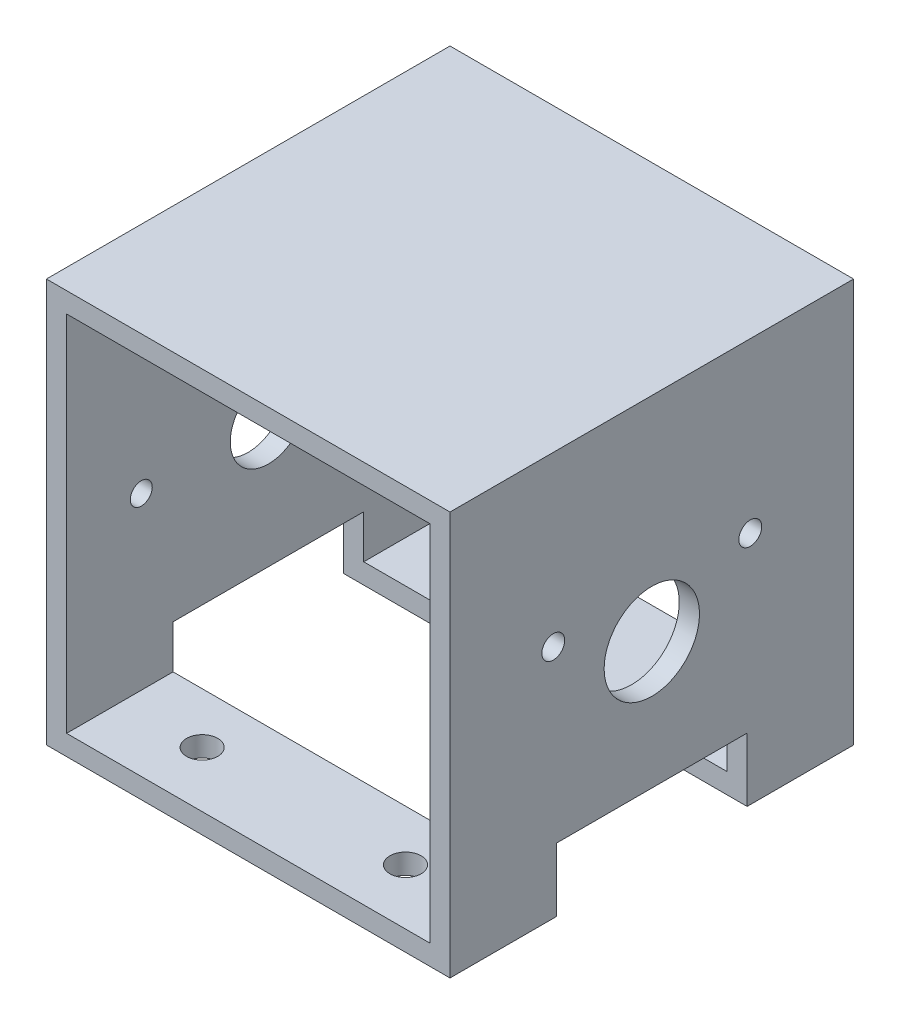
SolidWorks part; units mm, degrees
ref_plane "Front Plane" through (0, 0, 0) normal (0, 0, 1) x (1, 0, 0)
ref_plane "Top Plane" through (0, 0, 0) normal (0, 1, 0) x (1, 0, 0)
ref_plane "Right Plane" through (0, 0, 0) normal (1, 0, 0) x (0, 0, -1)
sketch "Sketch1" plane through (0, 0, 0) normal (0, 0, 1) x (1, 0, 0)
  line L1 (-31.75, -31.75) -> (31.75, -31.75)
  line L2 (-31.75, -31.75) -> (-31.75, 31.75)
  line L3 (-31.75, 31.75) -> (31.75, 31.75)
  line L4 (31.75, -31.75) -> (31.75, 31.75)
  line L5 (-31.75, -31.75) -> (31.75, 31.75) construction
  line L6 (-31.75, 31.75) -> (31.75, -31.75) construction
  point P0 (0, 0)
  dimension "D1" = 63.5
extrude "Extrude-Thin1" add sketch "Sketch1" along normal blind 63.5 thin thin type one direction reverse wall 3.175
sketch "Sketch2" plane through (31.75, 0, 0) normal (1, 0, 0) x (0, 0, -1)
  line L0 (-63.5, -31.75) -> (0, -31.75) construction
  line L1 (-16.75, -41.75) -> (-46.75, -41.75)
  line L2 (-16.75, -41.75) -> (-16.75, -21.75)
  line L3 (-16.75, -21.75) -> (-46.75, -21.75)
  line L4 (-46.75, -41.75) -> (-46.75, -21.75)
  line L5 (-16.75, -41.75) -> (-46.75, -21.75) construction
  line L6 (-16.75, -21.75) -> (-46.75, -41.75) construction
  point P0 (-31.75, -31.75)
  dimension "D1" = 30
  dimension "D2" = 10
extrude "Cut-Extrude1" cut sketch "Sketch2" against normal through all contours L1 L4 L3 L2
sketch "Sketch5" plane through (28.575, 11.8301, 29.9884) normal (-1, 0, 0) x (0, 0, 1)
  line L0 (1.7616, -13.5801) -> (1.7616, -33.5801) construction
  line L1 (16.7616, -33.5801) -> (-13.2384, -33.5801) construction
  circle A0 centre (1.7616, -13.5801) radius 7.5
  dimension "D1" = 15
  dimension "D2" = 20
extrude "Cut-Extrude3" cut sketch "Sketch5" against normal through all
hole_wizard "M3 Clearance Hole1" positions "Sketch7" profile "Sketch9" hole size "M3" standard "ANSI Metric"
sketch "Sketch7" plane through (28.575, 11.8301, 29.9884) normal (-1, 0, 0) x (0, 0, 1)
  line L0 (-13.7384, -6.5801) -> (17.2616, -6.5801)
  line L2 (-6.1211, -20.0801) -> (-6.1211, 6.9199)
  line L4 (-6.1211, 6.9199) -> (17.2616, -6.5801)
  line L8 (1.7616, -13.5801) -> (1.7616, -6.5801) construction
  line L11 (1.7616, -6.5801) -> (-6.1211, -6.5801)
  circle A0 centre (1.7616, -6.5801) radius 18.5
  circle A2 centre (1.7616, -13.5801) radius 7.5 construction
  point P0 (-13.7384, -6.5801)
  point P2 (17.2616, -6.5801)
  dimension "D4" = 37
  dimension "D1" = 31
  dimension "D2" = 27
  dimension "D3" = 7
sketch "Sketch9" plane through (28.575, 5.25, 16.25) normal (0, 1, 0) x (0, 0, 1)
  line L0 (0, 0) -> (0, 3.175)
  line L1 (0, 3.175) -> (1.8, 3.175)
  line L2 (1.8, 3.175) -> (1.8, 0)
  line L5 (1.8, 0) -> (0, 0)
  line L11 (0, -6.35) -> (0, 107.95) construction
  dimension "Thru Hole Dia." = 3.6
  dimension "Thru Hole Depth" = 3.175
hole_wizard "#8-32 Tapped Hole1" positions "Sketch12" profile "Sketch11" tap size "#8-32" standard "ANSI Inch" end condition up to next
sketch "Sketch12" plane through (-31.75, 0, 0) normal (-1, 0, 0) x (0, 0, 1)
  line L0 (11.75, -1.75) -> (51.75, -1.75)
  circle A0 centre (31.75, -1.75) radius 7.5 construction
  circle A1 centre (31.75, -1.75) radius 7.5
  point P0 (51.75, -1.75)
  point P2 (11.75, -1.75)
  dimension "D1" = 40
sketch "Sketch11" plane through (-31.75, -1.75, 51.75) normal (0, 1, 0) x (0, 0, 1)
  line L0 (0, 0) -> (0, 3.175)
  line L1 (0, 3.175) -> (1.7272, 3.175)
  line L2 (1.7272, 3.175) -> (1.7272, 0)
  line L5 (1.7272, 0) -> (0, 0)
  line L11 (0, -6.35) -> (0, 107.95) construction
  dimension "Thru Tap Drill Dia." = 3.4544
  dimension "Thru Tap Drill Depth" = 3.175
cosmetic thread "Hole Thread1" parameters "D2"=4.1656
cosmetic thread "Hole Thread2" parameters "D2"=4.1656
sketch "Sketch13" plane through (-31.75, 0, 0) normal (-1, 0, 0) x (0, 0, 1)
  circle A0 centre (31.75, -1.75) radius 7.5 construction
  circle A1 centre (31.75, -1.75) radius 7.5 construction
  circle A2 centre (31.75, -1.75) radius 6
  dimension "D1" = 12
extrude "Cut-Extrude4" cut sketch "Sketch13" against normal up to next
hole_wizard "#8 Clearance Hole1" positions "Sketch15" profile "Sketch14" hole size "#8" standard "ANSI Inch" end condition up to next
sketch "Sketch15" plane through (0, -31.75, 0) normal (0, -1, 0) x (-1, 0, 0)
  line L0 (-16, -8.75) -> (16, -8.75)
  line L1 (16, -8.75) -> (16, -54.75)
  line L2 (16, -54.75) -> (-16, -54.75)
  line L3 (-16, -54.75) -> (-16, -8.75)
  line L23 (0, -8.75) -> (0, 0)
  line L24 (31.75, 0) -> (-31.75, 0) construction
  line L29 (31.75, -46.75) -> (31.75, -16.75)
  line L31 (16, -31.75) -> (31.75, -31.75)
  point P0 (16, -8.75)
  point P2 (-16, -8.75)
  point P4 (-16, -54.75)
  point P6 (16, -54.75)
  dimension "D1" = 32
  dimension "D2" = 46
sketch "Sketch14" plane through (-16, -31.75, 8.75) normal (1, 0, 0) x (0, 0, -1)
  line L0 (0, 0) -> (0, 3.175)
  line L1 (0, 3.175) -> (2.4574, 3.175)
  line L2 (2.4574, 3.175) -> (2.4574, 0)
  line L5 (2.4574, 0) -> (0, 0)
  line L11 (0, -6.35) -> (0, 107.95) construction
  dimension "Thru Hole Dia." = 4.9149
  dimension "Thru Hole Depth" = 3.175
